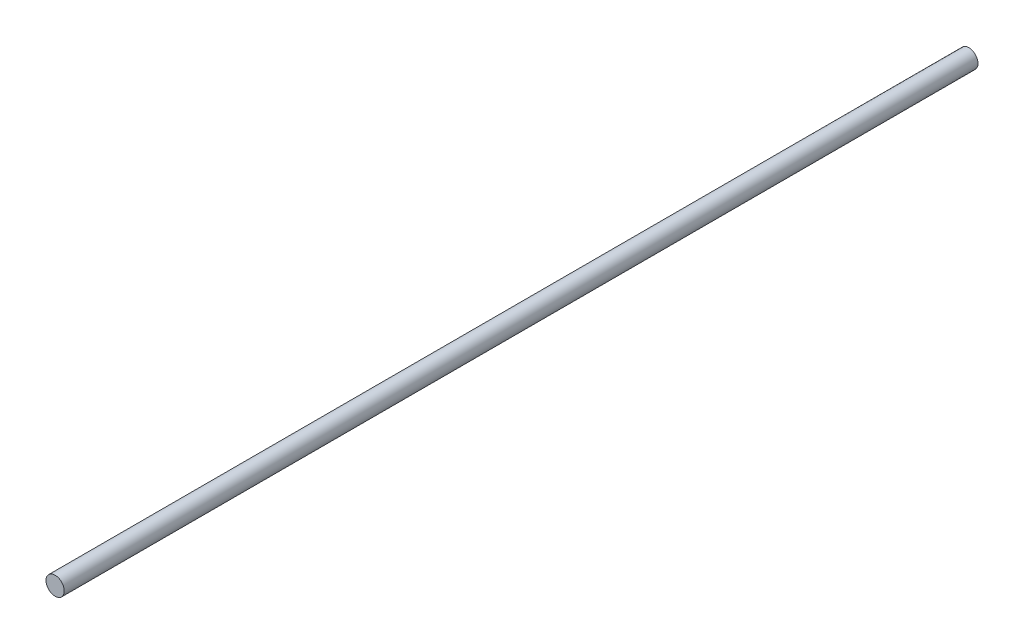
SolidWorks part; units mm, degrees
ref_plane "Front Plane" through (0, 0, 0) normal (0, 0, 1) x (1, 0, 0)
ref_plane "Top Plane" through (0, 0, 0) normal (0, 1, 0) x (1, 0, 0)
ref_plane "Right Plane" through (0, 0, 0) normal (1, 0, 0) x (0, 0, -1)
sketch "Sketch1" plane through (0, 0, 0) normal (0, 0, 1) x (1, 0, 0)
  circle A0 centre (0, 0) radius 2
  dimension "D1" = 4
extrude "Boss-Extrude1" add sketch "Sketch1" along normal mid plane 200
